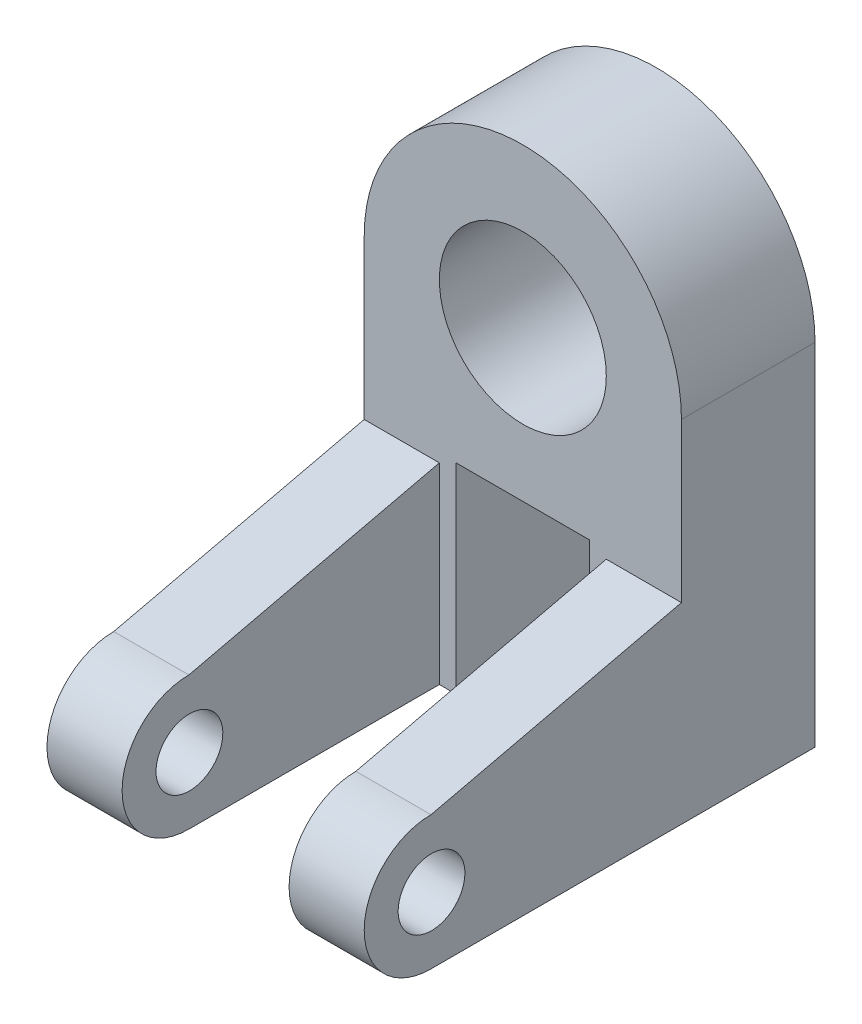
SolidWorks part; units mm, degrees
ref_plane "Front Plane" through (0, 0, 0) normal (0, 0, 1) x (1, 0, 0)
ref_plane "Top Plane" through (0, 0, 0) normal (0, 1, 0) x (1, 0, 0)
ref_plane "Right Plane" through (0, 0, 0) normal (1, 0, 0) x (0, 0, -1)
sketch "Sketch1" plane through (0, 0, 0) normal (0, 0, 1) x (1, 0, 0)
  line L0 (0, 49.3953) -> (0, -111.3857) construction
  line L1 (-74.74, 0) -> (82.5032, 0) construction
  line L2 (-38, 0) -> (-38, -84)
  line L3 (38, 0) -> (38, -84)
  line L8 (-38, -84) -> (-16, -84)
  line L9 (38, -84) -> (16, -84)
  line L10 (-16, -84) -> (-16, -36)
  line L11 (16, -84) -> (16, -36)
  line L12 (-16, -36) -> (16, -36)
  arc A0 (38, 0) -> (-38, 0) centre (0, 0) ccw
  dimension "D1" = 84
  dimension "D3" = 38
  dimension "D5" = 22
  dimension "D6" = 48
extrude "Boss-Extrude1" add sketch "Sketch1" along normal blind 32
sketch "Sketch2" plane through (0, 0, 32) normal (0, 0, 1) x (1, 0, 0)
  line L0 (0, 70.6775) -> (0, -114.7485) construction
  line L1 (-138.1652, 0) -> (135.0306, 0) construction
  circle A0 centre (0, 0) radius 20
extrude "Cut-Extrude1" cut sketch "Sketch2" against normal through all
sketch "Sketch3" plane through (-38, 0, 0) normal (-1, 0, 0) x (0, 0, 1)
  line L0 (32, -84) -> (92, -84)
  line L1 (92, -19.676) -> (92, -142.6069) construction
  line L2 (141.1694, -68) -> (-10.3214, -68) construction
  line L5 (92, -52) -> (32, -38)
  line L6 (32, 0) -> (32, -84) construction
  line L9 (0, 0) -> (0, -84)
  line L10 (0, -84) -> (32, -84)
  line L11 (32, -84) -> (32, 0)
  line L12 (32, 0) -> (0, 0)
  line L15 (32, -84) -> (32, -38)
  arc A0 (92, -84) -> (92, -52) centre (92, -68) ccw
  dimension "D1" = 16
  dimension "D2" = 60
  dimension "D3" = 0
extrude "Boss-Extrude2" add sketch "Sketch3" against normal blind 18
mirror "Mirror1" about plane through (0, 0, 0) normal (1, 0, 0) of "Boss-Extrude2"
hole_wizard "Ø16.0mm Dowel Slot1" positions "Sketch11" profile "Sketch10" size "Ø16.0" standard "ANSI Metric" slot yes end condition through all
sketch "Sketch11" plane through (-38, 0, 0) normal (-1, 0, 0) x (0, 0, 1)
  point P0 (91.8773, -68.136)
  point P2 (91.8773, -68.136)
sketch "Sketch10" plane through (-38, -68.136, 91.8773) normal (0, 1, 0) x (0, 0, 1)
  line L0 (0, 0) -> (0, 76)
  line L1 (0, 76) -> (8, 76)
  line L2 (8, 76) -> (8, 0)
  line L5 (8, 0) -> (0, 0)
  line L11 (0, -6.35) -> (0, 107.95) construction
  dimension "Thru Hole Dia." = 16
  dimension "Thru Hole Depth" = 76
